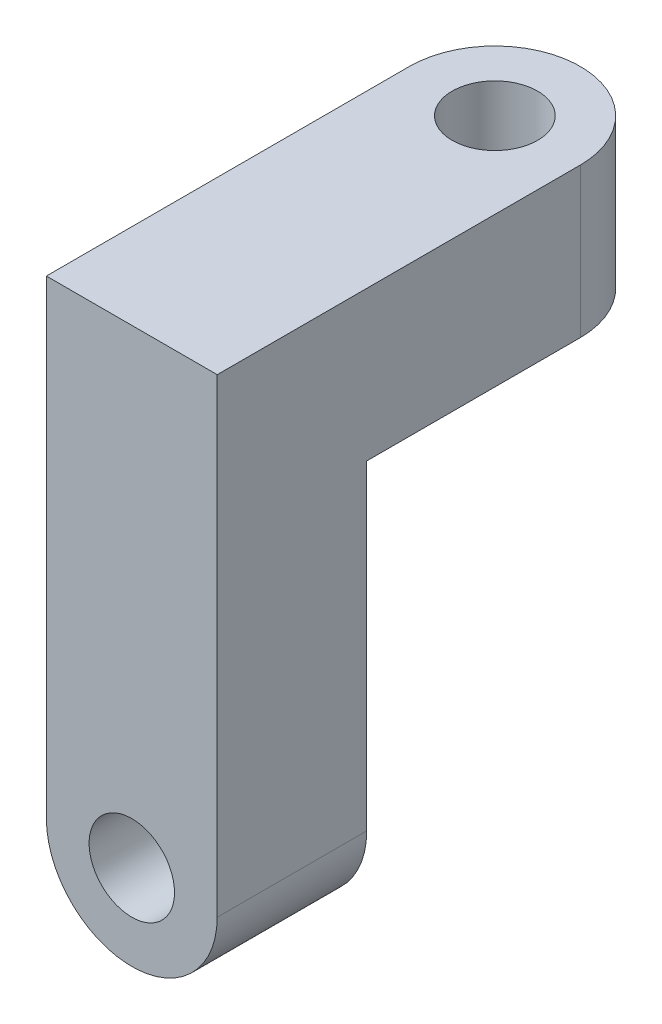
SolidWorks part; units mm, degrees
ref_plane "Front Plane" through (0, 0, 0) normal (0, 0, 1) x (1, 0, 0)
ref_plane "Top Plane" through (0, 0, 0) normal (0, 1, 0) x (1, 0, 0)
ref_plane "Right Plane" through (0, 0, 0) normal (1, 0, 0) x (0, 0, -1)
sketch "Sketch2" plane through (0, 0, 0) normal (0, 0, 1) x (1, 0, 0)
  line L1 (-4, -15) -> (-4, 0)
  line L2 (-4, 0) -> (4, 0)
  line L3 (4, 0) -> (4, -15)
  circle A0 centre (0, -15) radius 1.5
  arc A1 (-4, -15) -> (4, -15) centre (0, -15) ccw
extrude "Boss-Extrude1" add sketch "Sketch2" along normal blind 7
sketch "Sketch3" plane through (0, 0, 0) normal (0, 1, 0) x (1, 0, 0)
  line L0 (0, 0) -> (0, 10)
  line L1 (-4, 10) -> (-4, -7)
  line L2 (-4, -7) -> (4, -7)
  line L3 (4, -7) -> (4, 10)
  circle A0 centre (0, 10) radius 1.5
  arc A1 (4, 10) -> (-4, 10) centre (0, 10) ccw
extrude "Boss-Extrude2" add sketch "Sketch3" along normal blind 7
sketch "Sketch4" plane through (0, 7, 0) normal (0, 1, 0) x (1, 0, 0)
  circle A0 centre (0, 10) radius 2
sketch "Sketch5" plane through (0, 0, 7) normal (0, 0, 1) x (1, 0, 0)
  circle A0 centre (0, -15) radius 2
extrude "Cut-Extrude1" cut sketch "Sketch4" against normal blind 10
extrude "Cut-Extrude2" cut sketch "Sketch5" against normal blind 10
